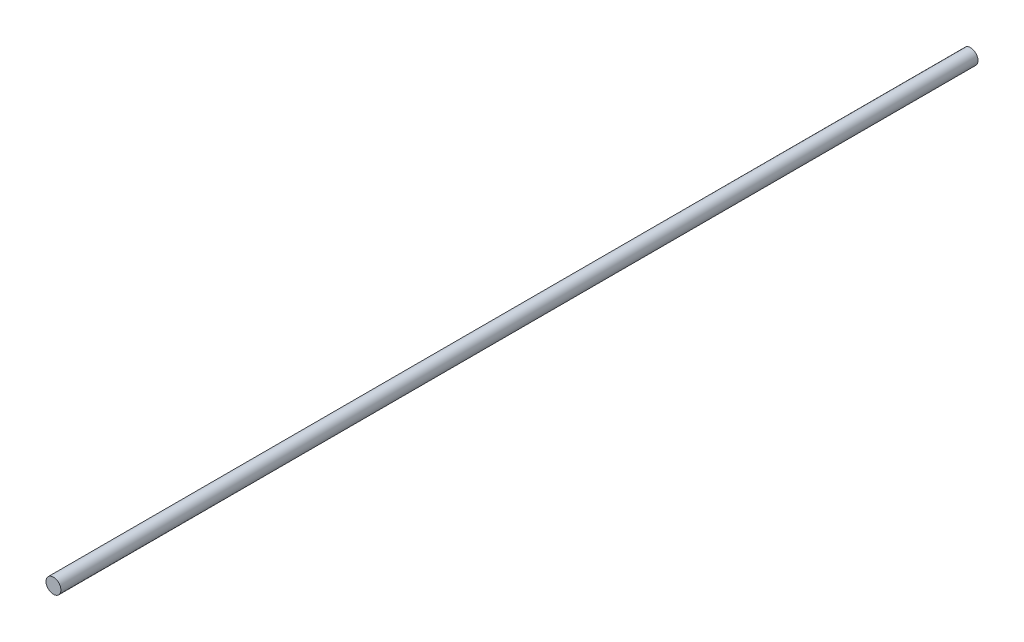
SolidWorks part; units mm, degrees
material "AISI 1010 Steel, hot rolled bar"
ref_plane "Front Plane" through (0, 0, 0) normal (0, 0, 1) x (1, 0, 0)
ref_plane "Top Plane" through (0, 0, 0) normal (0, 1, 0) x (1, 0, 0)
ref_plane "Right Plane" through (0, 0, 0) normal (1, 0, 0) x (0, 0, -1)
sketch "Sketch1" plane through (0, 0, 0) normal (0, 0, 1) x (1, 0, 0)
  circle A0 centre (0, 0) radius 5
  dimension "D1" = 10
extrude "Boss-Extrude1" add sketch "Sketch1" along normal mid plane 615
